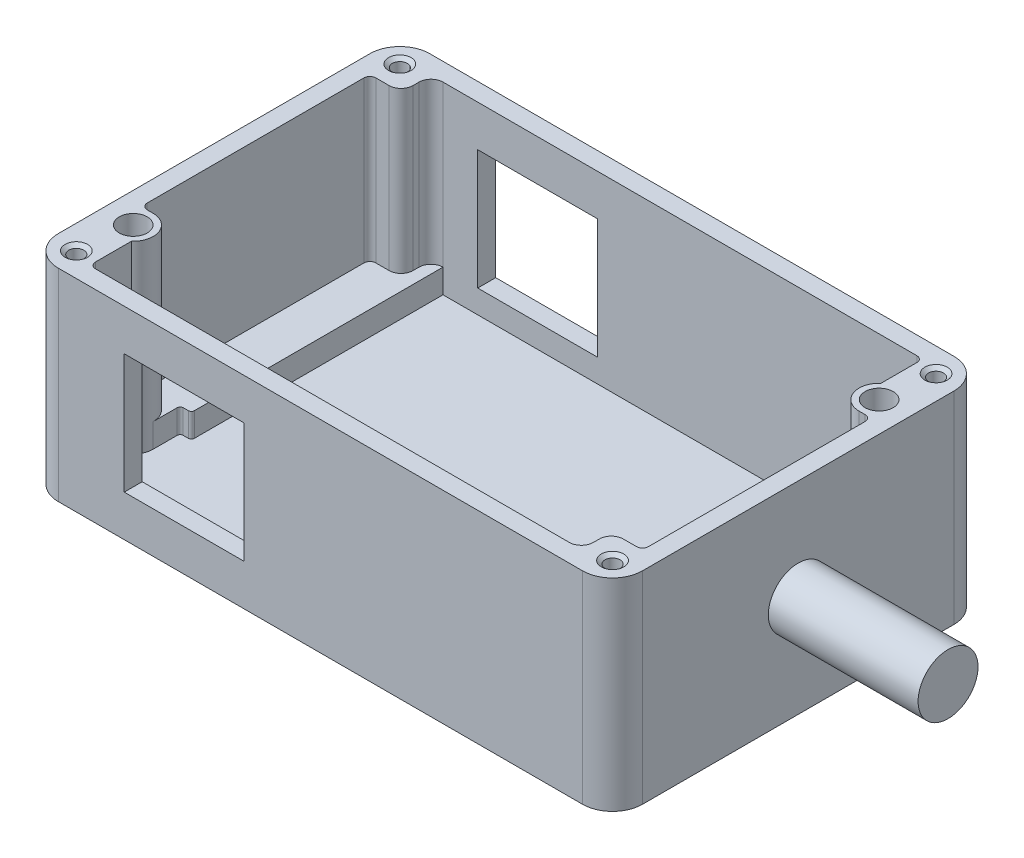
SolidWorks part; units mm, degrees
ref_plane "Front Plane" through (0, 0, 0) normal (0, 0, 1) x (1, 0, 0)
ref_plane "Top Plane" through (0, 0, 0) normal (0, 1, 0) x (1, 0, 0)
ref_plane "Right Plane" through (0, 0, 0) normal (1, 0, 0) x (0, 0, -1)
sketch "Sketch1" plane through (0, 0, 0) normal (0, 1, 0) x (1, 0, 0)
  line L1 (6.35, 0) -> (117.475, 0)
  line L2 (0, 6.35) -> (0, 72.39)
  line L3 (6.35, 78.74) -> (117.475, 78.74)
  line L4 (123.825, 6.35) -> (123.825, 72.39)
  arc A0 (117.475, 78.74) -> (123.825, 72.39) centre (117.475, 72.39) cw
  arc A1 (123.825, 6.35) -> (117.475, 0) centre (117.475, 6.35) cw
  arc A2 (6.35, 0) -> (0, 6.35) centre (6.35, 6.35) cw
  arc A3 (0, 72.39) -> (6.35, 78.74) centre (6.35, 72.39) cw
  point P11 (0, 0)
  dimension "D1" = 6.35
extrude "Boss-Extrude1" add sketch "Sketch1" along normal blind 42.8625
hole_wizard "CSK for #0 Flat Head Machine Screw (100)1" positions "Sketch3" profile "Sketch4" countersink size "#0" standard "ANSI Inch" end condition through all
sketch "Sketch3" plane through (0, 42.8625, 0) normal (0, 1, 0) x (1, 0, 0)
  line L0 (117.475, 78.74) -> (6.35, 78.74) construction
  line L1 (0, 72.39) -> (0, 6.35) construction
  line L2 (6.35, 0) -> (117.475, 0) construction
  line L3 (123.825, 6.35) -> (123.825, 72.39) construction
  point P0 (5.08, 5.08)
  point P1 (5.08, 73.66)
  point P3 (118.745, 73.66)
  point P5 (118.745, 5.08)
  dimension "D1" = 5.08
  dimension "D2" = 5.08
  dimension "D3" = 5.08
  dimension "D4" = 5.08
  dimension "D5" = 5.08
  dimension "D6" = 5.08
  dimension "D7" = 5.08
  dimension "D8" = 5.08
sketch "Sketch4" plane through (5.08, 42.8625, -5.08) normal (1, 0, 0) x (0, 0, 1)
  line L0 (0, 0) -> (0, 42.8625)
  line L1 (0, 42.8625) -> (1.5875, 42.8625)
  line L2 (1.5875, 42.8625) -> (1.5875, 0.666)
  line L3 (1.5875, 0.666) -> (2.3813, 0)
  line L5 (2.3813, 0) -> (0, 0)
  line L6 (-1.5875, 0.666) -> (-2.3813, 0) construction
  line L11 (0, -6.35) -> (0, 107.95) construction
  dimension "Thru Hole Dia." = 3.175
  dimension "Thru Hole Depth" = 42.8625
  dimension "Near C'Sink Dia." = 4.7625
  dimension "Near C'Sink Angle" = 100
hole_wizard "A (0.234) Diameter Hole1" positions "Sketch7" profile "Sketch8" hole size "A" standard "ANSI Inch" end condition up to next
sketch "Sketch7" plane through (0, 42.8625, 0) normal (0, 1, 0) x (1, 0, 0)
  line L7 (6.35, 0) -> (117.475, 0) construction
  line L9 (0, 72.39) -> (0, 6.35) construction
  line L10 (123.825, 6.35) -> (123.825, 72.39) construction
  line L11 (117.475, 78.74) -> (6.35, 78.74) construction
  point P4 (6.35, 15.875)
  point P15 (117.475, 62.865)
  dimension "D1" = 6.35
  dimension "D2" = 15.875
  dimension "D3" = 6.35
  dimension "D4" = 15.875
sketch "Sketch8" plane through (6.35, 42.8625, -15.875) normal (1, 0, 0) x (0, 0, 1)
  line L0 (0, 0) -> (0, 42.8625)
  line L1 (0, 42.8625) -> (2.9718, 42.8625)
  line L2 (2.9718, 42.8625) -> (2.9718, 0)
  line L5 (2.9718, 0) -> (0, 0)
  line L11 (0, -6.35) -> (0, 107.95) construction
  dimension "Thru Hole Dia." = 5.9436
  dimension "Thru Hole Depth" = 42.8625
sketch "Sketch9" plane through (0, 42.8625, 0) normal (0, 1, 0) x (1, 0, 0)
  line L0 (5.08, 68.58) -> (7.8806, 68.58)
  line L1 (0, 72.39) -> (0, 6.35) construction
  line L3 (3.81, 21.3868) -> (3.81, 67.31)
  line L5 (6.35, 0) -> (117.475, 0) construction
  line L9 (110.8644, 3.81) -> (61.9125, 3.81)
  line L10 (10.4206, 72.39) -> (10.4206, 71.12)
  line L11 (12.9606, 74.93) -> (61.9125, 74.93)
  line L12 (118.745, 10.16) -> (115.9444, 10.16)
  line L13 (5.08, 20.1168) -> (6.35, 20.1168)
  line L14 (9.1506, 12.6892) -> (9.1506, 5.08)
  line L15 (10.4206, 3.81) -> (61.9125, 3.81)
  line L16 (120.015, 57.3532) -> (120.015, 11.43)
  line L17 (113.4044, 6.35) -> (113.4044, 7.62)
  line L18 (118.745, 58.6232) -> (117.475, 58.6232)
  line L19 (114.6744, 66.0508) -> (114.6744, 73.66)
  line L20 (113.4044, 74.93) -> (61.9125, 74.93)
  arc A3 (10.4206, 3.81) -> (9.1506, 5.08) centre (10.4206, 5.08) cw
  arc A4 (6.35, 20.1168) -> (9.1506, 12.6892) centre (6.35, 15.875) cw
  arc A6 (5.08, 20.1168) -> (3.81, 21.3868) centre (5.08, 21.3868) cw
  arc A8 (5.08, 68.58) -> (3.81, 67.31) centre (5.08, 67.31) ccw
  arc A9 (10.4206, 71.12) -> (7.8806, 68.58) centre (7.8806, 71.12) cw
  arc A11 (12.9606, 74.93) -> (10.4206, 72.39) centre (12.9606, 72.39) ccw
  arc A12 (118.745, 10.16) -> (120.015, 11.43) centre (118.745, 11.43) ccw
  arc A13 (113.4044, 7.62) -> (115.9444, 10.16) centre (115.9444, 7.62) cw
  arc A14 (110.8644, 3.81) -> (113.4044, 6.35) centre (110.8644, 6.35) ccw
  arc A15 (118.745, 58.6232) -> (120.015, 57.3532) centre (118.745, 57.3532) cw
  arc A16 (117.475, 58.6232) -> (114.6744, 66.0508) centre (117.475, 62.865) cw
  arc A17 (113.4044, 74.93) -> (114.6744, 73.66) centre (113.4044, 73.66) cw
  point P28 (9.1506, 3.81)
  point P61 (61.9125, 39.37)
  dimension "D1" = 3.81
  dimension "D4" = 1.27
  dimension "D6" = 1.27
  dimension "D3" = 2.54
  dimension "D5" = 2.54
  dimension "D2" = 3.81
  dimension "D7" = 2
extrude "Cut-Extrude1" cut sketch "Sketch9" against normal blind 39.0525
sketch "Sketch11" plane through (0, 3.81, 0) normal (0, 1, 0) x (1, 0, 0)
  line L0 (12.9606, 74.93) -> (12.9606, 22.225)
  line L1 (12.3256, 21.59) -> (11.2268, 21.59)
  line L2 (10.5918, 20.955) -> (10.5918, 15.875)
  line L13 (110.8644, 3.81) -> (110.8644, 56.515)
  line L14 (111.4994, 57.15) -> (112.5982, 57.15)
  line L15 (113.2332, 57.785) -> (113.2332, 62.865)
  line L16 (117.475, 58.6232) -> (118.745, 58.6232)
  line L17 (6.35, 20.1168) -> (5.08, 20.1168)
  line L18 (3.81, 21.3868) -> (3.81, 67.31)
  line L19 (5.08, 68.58) -> (7.8806, 68.58)
  line L20 (10.4206, 71.12) -> (10.4206, 72.39)
  line L21 (6.35, 20.1168) -> (5.08, 20.1168)
  line L22 (3.81, 21.3868) -> (3.81, 67.31)
  line L23 (5.08, 68.58) -> (7.8806, 68.58)
  line L24 (10.4206, 71.12) -> (10.4206, 72.39)
  line L25 (120.015, 57.3532) -> (120.015, 11.43)
  line L26 (118.745, 10.16) -> (115.9444, 10.16)
  line L27 (113.4044, 7.62) -> (113.4044, 6.35)
  arc A3 (9.1506, 12.6892) -> (6.35, 20.1168) centre (6.35, 15.875) ccw construction
  arc A4 (9.1506, 12.6892) -> (6.35, 20.1168) centre (6.35, 15.875) ccw construction
  arc A5 (11.2268, 21.59) -> (10.5918, 20.955) centre (11.2268, 20.955) ccw
  arc A6 (12.3256, 21.59) -> (12.9606, 22.225) centre (12.3256, 22.225) ccw
  arc A9 (112.5982, 57.15) -> (113.2332, 57.785) centre (112.5982, 57.785) ccw
  arc A10 (111.4994, 57.15) -> (110.8644, 56.515) centre (111.4994, 56.515) ccw
  arc A11 (113.2332, 62.865) -> (117.475, 58.6232) centre (117.475, 62.865) ccw
  arc A12 (120.015, 57.3532) -> (118.745, 58.6232) centre (118.745, 57.3532) ccw
  arc A13 (118.745, 10.16) -> (120.015, 11.43) centre (118.745, 11.43) ccw
  arc A14 (9.1506, 12.6892) -> (6.35, 20.1168) centre (6.35, 15.875) ccw
  arc A15 (3.81, 21.3868) -> (5.08, 20.1168) centre (5.08, 21.3868) ccw
  arc A16 (5.08, 68.58) -> (3.81, 67.31) centre (5.08, 67.31) ccw
  arc A17 (7.8806, 68.58) -> (10.4206, 71.12) centre (7.8806, 71.12) ccw
  arc A18 (12.9606, 74.93) -> (10.4206, 72.39) centre (12.9606, 72.39) ccw
  arc A19 (10.5918, 15.875) -> (6.35, 20.1168) centre (6.35, 15.875) ccw
  arc A20 (3.81, 21.3868) -> (5.08, 20.1168) centre (5.08, 21.3868) ccw
  arc A21 (5.08, 68.58) -> (3.81, 67.31) centre (5.08, 67.31) ccw
  arc A22 (7.8806, 68.58) -> (10.4206, 71.12) centre (7.8806, 71.12) ccw
  arc A23 (12.9606, 74.93) -> (10.4206, 72.39) centre (12.9606, 72.39) ccw
  arc A24 (115.9444, 10.16) -> (113.4044, 7.62) centre (115.9444, 7.62) ccw
  arc A25 (110.8644, 3.81) -> (113.4044, 6.35) centre (110.8644, 6.35) ccw
  point P65 (61.9125, 39.37)
  dimension "D1" = 0.635
  dimension "D2" = 0
  dimension "D3" = 2
extrude "Boss-Extrude2" add sketch "Sketch11" along normal blind 5.08
sketch "Sketch12" plane through (0, 0, -78.74) normal (0, 0, -1) x (-1, 0, 0)
  line L1 (-45.72, 34.1312) -> (-20.32, 34.1312)
  line L2 (-45.72, 34.1312) -> (-45.72, 8.7312)
  line L3 (-45.72, 8.7312) -> (-20.32, 8.7312)
  line L4 (-20.32, 34.1312) -> (-20.32, 8.7312)
  line L5 (-45.72, 34.1312) -> (-20.32, 8.7312) construction
  line L6 (-45.72, 8.7312) -> (-20.32, 34.1312) construction
  point P0 (-33.02, 21.4312)
extrude "Cut-Extrude2" cut sketch "Sketch12" against normal through all
sketch "Sketch13" plane through (123.825, 0, 0) normal (1, 0, 0) x (0, 0, -1)
  circle A0 centre (39.37, 21.4312) radius 6.35
extrude "Boss-Extrude3" add sketch "Sketch13" along normal blind 31.75
